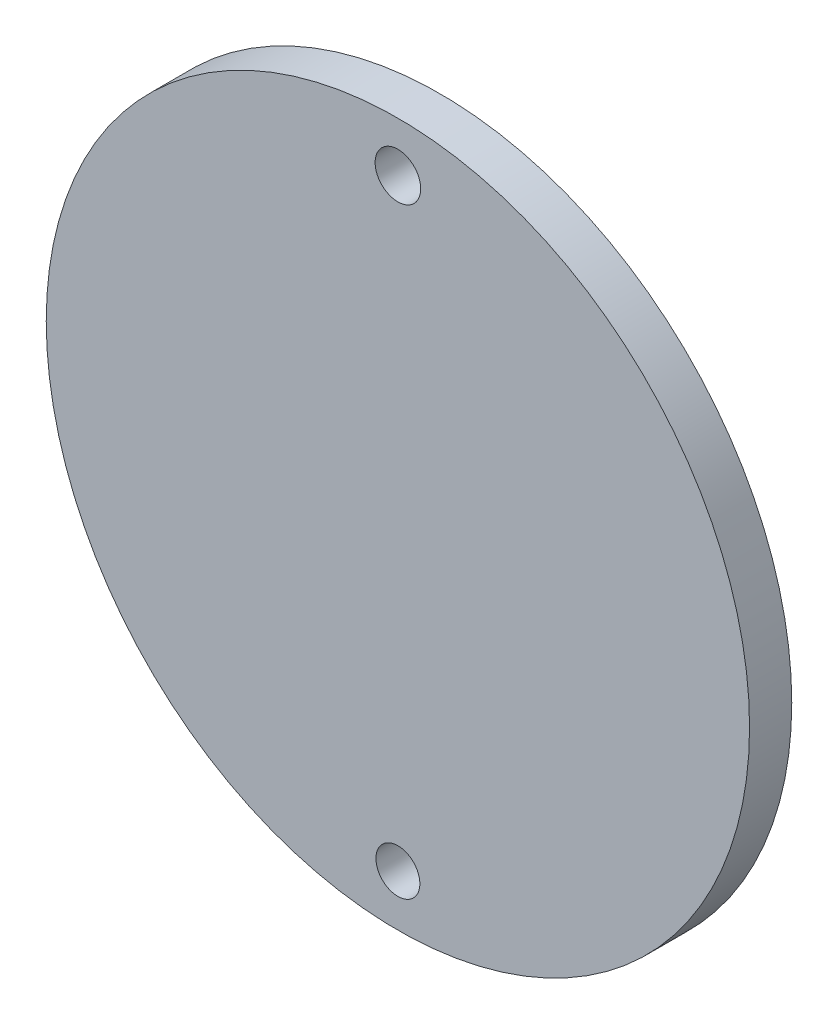
SolidWorks part; units mm, degrees
ref_plane "Front Plane" through (0, 0, 0) normal (0, 0, 1) x (1, 0, 0)
ref_plane "Top Plane" through (0, 0, 0) normal (0, 1, 0) x (1, 0, 0)
ref_plane "Right Plane" through (0, 0, 0) normal (1, 0, 0) x (0, 0, -1)
sketch "Sketch1" plane through (0, 0, 0) normal (0, 0, 1) x (1, 0, 0)
  circle A0 centre (32.4707, 38.3744) radius 25
  circle A1 centre (32.4707, 17.0194) radius 1.5612
  circle A2 centre (32.4707, 59.8346) radius 1.62
extrude "Boss-Extrude1" add sketch "Sketch1" along normal blind 3
